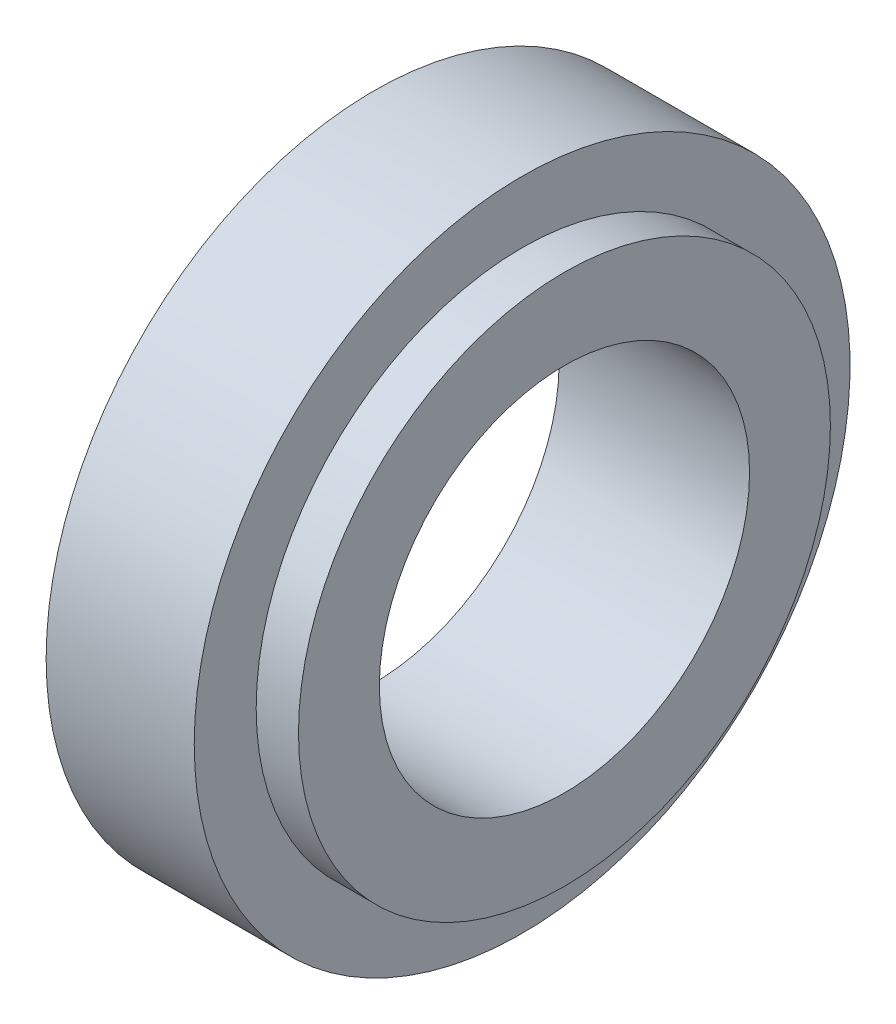
SolidWorks part; units mm, degrees
material "Plain Carbon Steel"
ref_plane "Front Plane" through (0, 0, 0) normal (0, 0, 1) x (1, 0, 0)
ref_plane "Top Plane" through (0, 0, 0) normal (0, 1, 0) x (1, 0, 0)
ref_plane "Right Plane" through (0, 0, 0) normal (1, 0, 0) x (0, 0, -1)
sketch "Sketch1" plane through (0, 0, 0) normal (0, 0, 1) x (1, 0, 0)
  line L0 (0, 0) -> (30.0376, 0) construction
  line L1 (0, 17.5) -> (18, 17.5)
  line L2 (18, 17.5) -> (18, 25.1437)
  line L3 (18, 25.1437) -> (14, 25.1437)
  line L4 (14, 25.1437) -> (14, 31)
  line L5 (14, 31) -> (0, 31)
  line L6 (0, 31) -> (0, 17.5)
  point P9 (0, 0)
  dimension "D1" = 35
  dimension "D2" = 18
  dimension "D3" = 14
  dimension "D4" = 62
revolve "Revolve1" add sketch "Sketch1" angle 360 about L0
